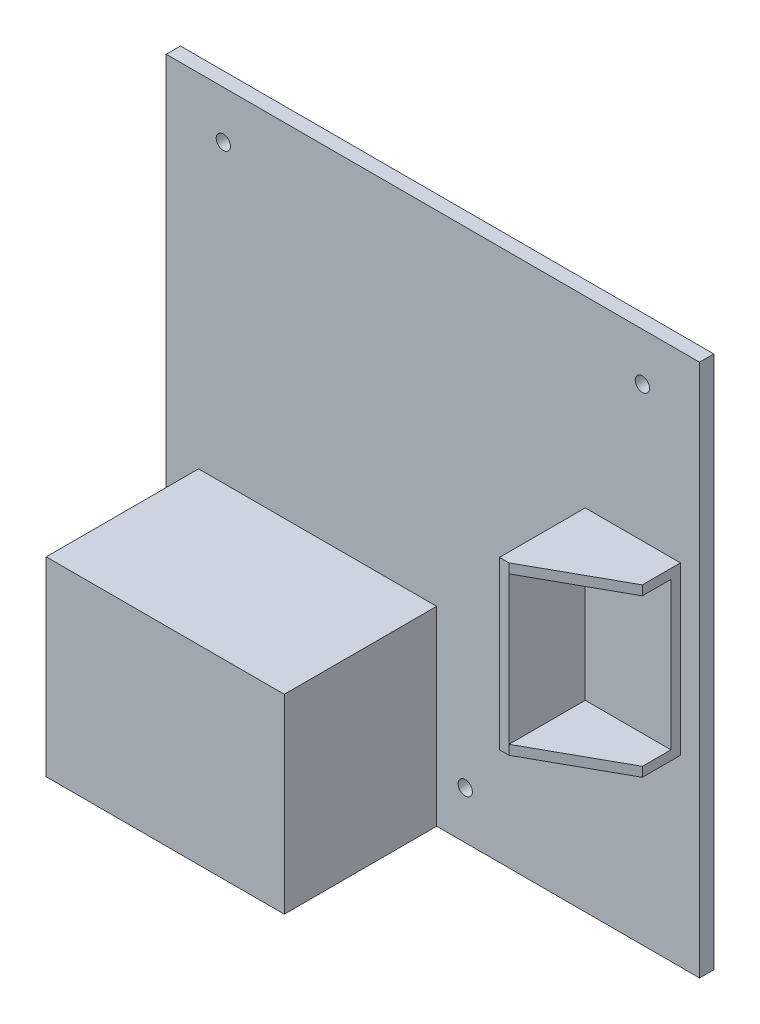
SolidWorks part; units mm, degrees
ref_plane "Front" through (0, 0, 0) normal (0, 0, 1) x (1, 0, 0)
ref_plane "Top" through (0, 0, 0) normal (0, 1, 0) x (1, 0, 0)
ref_plane "Right" through (0, 0, 0) normal (1, 0, 0) x (0, 0, -1)
sketch "Sketch1" plane through (0, 0, 0) normal (0, 0, 1) x (1, 0, 0)
  line L1 (-56, -56) -> (56, -56)
  line L2 (-56, -56) -> (-56, 56)
  line L3 (-56, 56) -> (56, 56)
  line L4 (56, -56) -> (56, 56)
  line L5 (-56, -56) -> (56, 56) construction
  line L6 (-56, 56) -> (56, -56) construction
  point P0 (0, 0)
  dimension "D1" = 112
extrude "Boss-Extrude1" add sketch "Sketch1" along normal blind 3
sketch "Sketch2" plane through (0, 0, 3) normal (0, 0, 1) x (1, 0, 0)
  line L0 (-56, -56) -> (56, -56) construction
  line L1 (-49.1968, -56) -> (0.8032, -56)
  line L2 (-49.1968, -56) -> (-49.1968, -16)
  line L3 (-49.1968, -16) -> (0.8032, -16)
  line L4 (0.8032, -56) -> (0.8032, -16)
  line L5 (-49.1968, -56) -> (0.8032, -16) construction
  line L6 (-49.1968, -16) -> (0.8032, -56) construction
  point P4 (-24.1968, -36)
  dimension "D1" = 40
  dimension "D2" = 50
extrude "Boss-Extrude2" add sketch "Sketch2" along normal blind 32
sketch "Sketch3" plane through (0, 0, 3) normal (0, 0, 1) x (1, 0, 0)
  line L0 (56, 56) -> (-56, 56) construction
  line L1 (-56, 56) -> (-56, -56) construction
  line L2 (56, -56) -> (56, 56) construction
  line L3 (0.8032, -56) -> (56, -56) construction
  line L4 (0.8032, -56) -> (0.8032, -16) construction
  circle A0 centre (-44, 46) radius 1.5
  circle A1 centre (44, 46) radius 1.5
  circle A2 centre (6.8032, -46) radius 1.5
  dimension "D1" = 3
  dimension "D2" = 3
  dimension "D3" = 10
  dimension "D4" = 12
  dimension "D5" = 12
  dimension "D6" = 3
  dimension "D7" = 10
  dimension "D8" = 6
extrude "Cut-Extrude1" cut sketch "Sketch3" against normal up to next
sketch "Sketch4" plane through (0, 0, 3) normal (0, 0, 1) x (1, 0, 0)
  line L0 (56, -56) -> (56, 56) construction
  line L1 (32, -17.5) -> (52, -17.5)
  line L2 (32, -17.5) -> (32, 17.5)
  line L3 (32, 17.5) -> (52, 17.5)
  line L4 (52, -17.5) -> (52, 17.5)
  line L5 (32, -17.5) -> (52, 17.5) construction
  line L6 (32, 17.5) -> (52, -17.5) construction
  point P0 (42, 0)
  dimension "D1" = 35
  dimension "D2" = 20
  dimension "D3" = 4
extrude "Boss-Extrude3" add sketch "Sketch4" along normal blind 18
sketch "Sketch5" plane through (0, 0, 21) normal (0, 0, 1) x (1, 0, 0)
  line L0 (52, 15.5) -> (34, 15.5)
  line L1 (34, 15.5) -> (34, -15.5)
  line L2 (34, -15.5) -> (52, -15.5)
  line L4 (52, -17.5) -> (52, 17.5)
  line L5 (52, 17.5) -> (32, 17.5)
  line L6 (32, 17.5) -> (32, -17.5)
  line L7 (32, -17.5) -> (52, -17.5)
  line L8 (52, -17.5) -> (52, 17.5)
  line L9 (52, 17.5) -> (32, 17.5)
  line L10 (32, 17.5) -> (32, -17.5)
  line L11 (32, -17.5) -> (52, -17.5)
  line L12 (50, 15.5) -> (34, 15.5) construction
  line L13 (34, -15.5) -> (50, -15.5) construction
  line L14 (50, -15.5) -> (50, 15.5) construction
  line M9 (52, -17.5) -> (52, 17.5)
  dimension "D1" = 0
  dimension "D2" = 2
extrude "Cut-Extrude2" cut sketch "Sketch5" against normal blind 16 contours L1 L2 L0 M9
sketch "Sketch6" plane through (0, 17.5, 0) normal (0, 1, 0) x (1, 0, 0)
  line L0 (34, -21) -> (52, -11)
  line L1 (52, -21) -> (32, -21) construction
  line L2 (52, -21) -> (52, -3) construction
  line L3 (34, -21) -> (52, -21)
  line L4 (52, -21) -> (52, -11)
  dimension "D1" = 8
  dimension "D2" = 2
extrude "Cut-Extrude3" cut sketch "Sketch6" against normal through all
